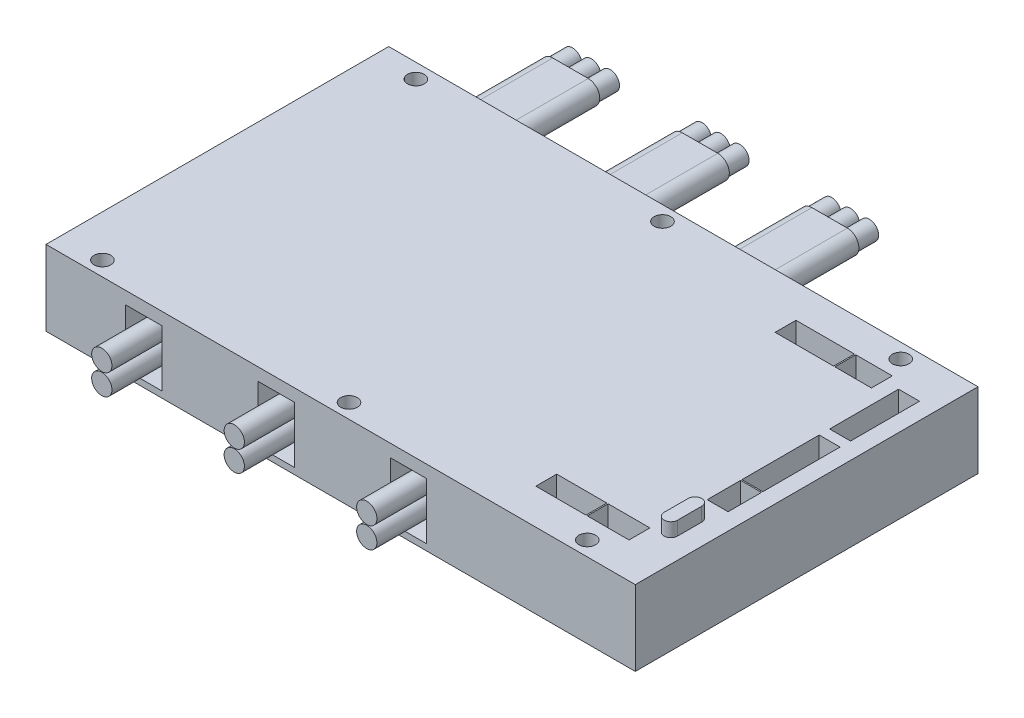
SolidWorks part; units mm, degrees
ref_plane "Front Plane" through (0, 0, 0) normal (0, 0, 1) x (1, 0, 0)
ref_plane "Top Plane" through (0, 0, 0) normal (0, 1, 0) x (1, 0, 0)
ref_plane "Right Plane" through (0, 0, 0) normal (1, 0, 0) x (0, 0, -1)
sketch "Sketch1" plane through (0, 0, 0) normal (0, 1, 0) x (1, 0, 0)
  line L1 (-70.5, -41) -> (70.5, -41)
  line L2 (-70.5, -41) -> (-70.5, 41)
  line L3 (-70.5, 41) -> (70.5, 41)
  line L4 (70.5, -41) -> (70.5, 41)
  line L5 (-70.5, -41) -> (70.5, 41) construction
  line L6 (-70.5, 41) -> (70.5, -41) construction
  point P0 (0, 0)
  dimension "D1" = 82
  dimension "D2" = 141
extrude "Boss-Extrude1" add sketch "Sketch1" along normal mid plane 18
sketch "Sketch3" plane through (0, 9, 0) normal (0, 1, 0) x (1, 0, 0)
  line L0 (-60.5, 37.5) -> (-1.5, 37.5) construction
  line L1 (-1.5, 37.5) -> (55.5, 37.5) construction
  line L2 (70.5, 41) -> (-70.5, 41) construction
  line L3 (-70.5, 41) -> (-70.5, -41) construction
  circle A0 centre (-60.5, 37.5) radius 2
  circle A1 centre (-1.5, 37.5) radius 2
  circle A2 centre (55.5, 37.5) radius 2
  dimension "D1" = 4
  dimension "D2" = 3.5
  dimension "D3" = 10
  dimension "D4" = 59
  dimension "D5" = 57
extrude "Cut-Extrude1" cut sketch "Sketch3" against normal through all
mirror "Mirror1" about plane through (0, 0, 0) normal (0, 0, 1) of "Cut-Extrude1"
sketch "Sketch4" plane through (0, 0, 41) normal (0, 0, 1) x (1, 0, 0)
  line L0 (-47.15, -0.75) -> (-15.45, -0.75) construction
  line L1 (-51.5, -7.5) -> (-42.8, -7.5)
  line L2 (-51.5, -7.5) -> (-51.5, 6)
  line L3 (-51.5, 6) -> (-42.8, 6)
  line L4 (-42.8, -7.5) -> (-42.8, 6)
  line L5 (-51.5, -7.5) -> (-42.8, 6) construction
  line L6 (-51.5, 6) -> (-42.8, -7.5) construction
  line L7 (-19.8, -7.5) -> (-11.1, -7.5)
  line L8 (-19.8, -7.5) -> (-19.8, 6)
  line L9 (-19.8, 6) -> (-11.1, 6)
  line L10 (-11.1, -7.5) -> (-11.1, 6)
  line L11 (-19.8, -7.5) -> (-11.1, 6) construction
  line L12 (-19.8, 6) -> (-11.1, -7.5) construction
  line L13 (11.9, -7.5) -> (20.6, -7.5)
  line L14 (11.9, -7.5) -> (11.9, 6)
  line L15 (11.9, 6) -> (20.6, 6)
  line L16 (20.6, -7.5) -> (20.6, 6)
  line L17 (11.9, -7.5) -> (20.6, 6) construction
  line L18 (11.9, 6) -> (20.6, -7.5) construction
  line L19 (-15.45, -0.75) -> (16.25, -0.75) construction
  line L20 (-70.5, 9) -> (70.5, 9) construction
  line L21 (-70.5, 9) -> (-70.5, -9) construction
  point P0 (-47.15, -0.75)
  point P5 (-15.45, -0.75)
  point P10 (16.25, -0.75)
  dimension "D1" = 13.5
  dimension "D2" = 8.7
  dimension "D3" = 3
  dimension "D4" = 19
  dimension "D5" = 23
extrude "Cut-Extrude2" cut sketch "Sketch4" against normal blind 10
sketch "Sketch5" plane through (0, 0, -41) normal (0, 0, -1) x (-1, 0, 0)
  line L0 (47, 3.5) -> (16, 3.5) construction
  line L1 (37, 1) -> (57, 1)
  line L2 (37, 1) -> (37, 6)
  line L3 (37, 6) -> (57, 6)
  line L4 (57, 1) -> (57, 6)
  line L5 (37, 1) -> (57, 6) construction
  line L6 (37, 6) -> (57, 1) construction
  line L7 (6, 1) -> (26, 1)
  line L8 (6, 1) -> (6, 6)
  line L9 (6, 6) -> (26, 6)
  line L10 (26, 1) -> (26, 6)
  line L11 (6, 1) -> (26, 6) construction
  line L12 (6, 6) -> (26, 1) construction
  line L13 (-25, 1) -> (-5, 1)
  line L14 (-25, 1) -> (-25, 6)
  line L15 (-25, 6) -> (-5, 6)
  line L16 (-5, 1) -> (-5, 6)
  line L17 (-25, 1) -> (-5, 6) construction
  line L18 (-25, 6) -> (-5, 1) construction
  line L19 (16, 3.5) -> (-15, 3.5) construction
  line L20 (-70.5, 9) -> (70.5, 9) construction
  line L21 (70.5, 9) -> (70.5, -9) construction
  point P0 (47, 3.5)
  point P5 (16, 3.5)
  point P10 (-15, 3.5)
  dimension "D1" = 3
  dimension "D2" = 5
  dimension "D3" = 20
  dimension "D4" = 13.5
  dimension "D5" = 11
extrude "Cut-Extrude3" cut sketch "Sketch5" against normal blind 10
sketch "Sketch6" plane through (0, 9, 0) normal (0, 1, 0) x (1, 0, 0)
  line L0 (-70.5, -41) -> (70.5, -41) construction
  line L1 (62.27, -25.885) -> (65.5, -25.885)
  line L2 (62.27, -25.885) -> (62.27, -20.115)
  line L3 (62.27, -20.115) -> (65.5, -20.115)
  line L4 (65.5, -25.885) -> (65.5, -20.115)
  line L5 (62.27, -25.885) -> (65.5, -20.115) construction
  line L6 (62.27, -20.115) -> (65.5, -25.885) construction
  line L7 (70.5, -41) -> (70.5, 41) construction
  arc A0 (65.5, -20.115) -> (62.27, -20.115) centre (63.885, -20.115) ccw
  arc A1 (65.5, -25.885) -> (62.27, -25.885) centre (63.885, -25.885) cw
  point P0 (63.885, -23)
  point P9 (63.885, -18.5)
  point P10 (63.885, -27.5)
  dimension "D1" = 3.23
  dimension "D2" = 9
  dimension "D3" = 13.5
  dimension "D4" = 5
extrude "Boss-Extrude2" add sketch "Sketch6" along normal blind 3.3 contours L1 L4 L3 L2 | L3 A0 | A1 L1
sketch "Sketch7" plane through (0, 0, 31) normal (0, 0, 1) x (1, 0, 0)
  line L0 (-47.15, 1.75) -> (-47.15, 6) construction
  line L1 (-42.8, 6) -> (-51.5, 6) construction
  line L2 (-47.15, 1.75) -> (-47.15, -3.25) construction
  line L3 (-47.15, -3.25) -> (-47.15, -7.5) construction
  line L4 (-51.5, -7.5) -> (-42.8, -7.5) construction
  circle A0 centre (-47.15, 1.75) radius 2.425
  circle A1 centre (-47.15, -3.25) radius 2.425
  dimension "D1" = 4.85
  dimension "D2" = 5
extrude "Boss-Extrude3" add sketch "Sketch7" along normal blind 20
pattern_linear "LPattern1" count 3 spacing 31.7 along (1, 0, 0) of "Boss-Extrude3"
sketch "Sketch8" plane through (0, 0, -31) normal (0, 0, -1) x (-1, 0, 0)
  line L0 (47, 3.5) -> (47, 6) construction
  line L1 (42.75, 0.75) -> (51.25, 0.75)
  line L2 (42.75, 0.75) -> (42.75, 6.25)
  line L3 (42.75, 6.25) -> (51.25, 6.25)
  line L4 (51.25, 0.75) -> (51.25, 6.25)
  line L5 (42.75, 0.75) -> (51.25, 6.25) construction
  line L6 (42.75, 6.25) -> (51.25, 0.75) construction
  line L7 (57, 6) -> (37, 6) construction
  line L8 (47, 3.5) -> (47, 1) construction
  line L9 (37, 1) -> (57, 1) construction
  arc A0 (51.25, 6.25) -> (51.25, 0.75) centre (51.25, 3.5) cw
  arc A1 (42.75, 6.25) -> (42.75, 0.75) centre (42.75, 3.5) ccw
  point P0 (47, 3.5)
  point P9 (40, 3.5)
  point P10 (54, 3.5)
  line M7 (57, 6) -> (37, 6)
  line M9 (37, 1) -> (57, 1)
  dimension "D1" = 14
  dimension "D2" = 5.5
extrude "Boss-Extrude4" add sketch "Sketch8" along normal blind 30 contours L4 L2 M9 M7 | A0 L4 M7 M9 | A1 L2 M7 M9 | L4 L3 L2 M7 | A0 L4 M7 | L2 A1 M7 | A1 L2 M9 | L1 L4 L2 M9 | A0 L4 M9
sketch "Sketch10" plane through (0, 0, -61) normal (0, 0, -1) x (-1, 0, 0)
  line L0 (42.75, 0.75) -> (51.25, 0.75) construction
  line L1 (42.75, 6.25) -> (51.25, 6.25) construction
  line L2 (42.75, 0.75) -> (51.25, 0.75) construction
  line L3 (42.75, 6.25) -> (51.25, 6.25) construction
  line L4 (42.5, 3.5) -> (47, 3.5) construction
  line L5 (47, 3.5) -> (51.5, 3.5) construction
  line L6 (47, 3.5) -> (47, 6.25) construction
  line L7 (47, 3.5) -> (47, 0.75) construction
  circle A0 centre (51.5, 3.5) radius 2.225
  circle A1 centre (47, 3.5) radius 2.225
  circle A2 centre (42.5, 3.5) radius 2.225
  dimension "D1" = 4.45
  dimension "D2" = 4.5
extrude "Boss-Extrude6" add sketch "Sketch10" along normal blind 5
pattern_linear "LPattern2" count 3 spacing 31 along (1, 0, 0) of "Boss-Extrude4", "Boss-Extrude6"
sketch "Sketch9" plane through (0, 9, 0) normal (0, 1, 0) x (1, 0, 0)
  line L0 (44.2, -30) -> (55.5, -30) construction
  line L1 (38.2, -32.5) -> (50.2, -32.5)
  line L2 (38.2, -32.5) -> (38.2, -27.5)
  line L3 (38.2, -27.5) -> (50.2, -27.5)
  line L4 (50.2, -32.5) -> (50.2, -27.5)
  line L5 (38.2, -32.5) -> (50.2, -27.5) construction
  line L6 (38.2, -27.5) -> (50.2, -32.5) construction
  line L11 (60.5, -32.5) -> (50.5, -32.5)
  line L12 (60.5, -32.5) -> (60.5, -27.5)
  line L13 (60.5, -27.5) -> (50.5, -27.5)
  line L14 (50.5, -32.5) -> (50.5, -27.5)
  line L15 (60.5, -32.5) -> (50.5, -27.5) construction
  line L16 (60.5, -27.5) -> (50.5, -32.5) construction
  line L17 (41.95, 30.5) -> (53.625, 30.5) construction
  line L18 (61.5, -14.8) -> (66.5, -14.8)
  line L19 (61.5, -14.8) -> (61.5, -6.8)
  line L20 (61.5, -6.8) -> (66.5, -6.8)
  line L21 (66.5, -14.8) -> (66.5, -6.8)
  line L22 (61.5, -14.8) -> (66.5, -6.8) construction
  line L23 (61.5, -6.8) -> (66.5, -14.8) construction
  line L24 (66.5, 12) -> (61.5, 12)
  line L25 (66.5, 12) -> (66.5, -6.5)
  line L26 (66.5, -6.5) -> (61.5, -6.5)
  line L27 (61.5, 12) -> (61.5, -6.5)
  line L28 (66.5, 12) -> (61.5, -6.5) construction
  line L29 (66.5, -6.5) -> (61.5, 12) construction
  line L30 (66.5, 31) -> (61.5, 31)
  line L31 (66.5, 31) -> (66.5, 14.5)
  line L32 (66.5, 14.5) -> (61.5, 14.5)
  line L33 (61.5, 31) -> (61.5, 14.5)
  line L34 (66.5, 31) -> (61.5, 14.5) construction
  line L35 (66.5, 14.5) -> (61.5, 31) construction
  line L36 (49.25, 28) -> (58, 28)
  line L37 (49.25, 28) -> (49.25, 33)
  line L38 (49.25, 33) -> (58, 33)
  line L39 (58, 28) -> (58, 33)
  line L40 (49.25, 28) -> (58, 33) construction
  line L41 (49.25, 33) -> (58, 28) construction
  line L42 (34.95, 28) -> (48.95, 28)
  line L43 (34.95, 28) -> (34.95, 33)
  line L44 (34.95, 33) -> (48.95, 33)
  line L45 (48.95, 28) -> (48.95, 33)
  line L46 (34.95, 28) -> (48.95, 33) construction
  line L47 (34.95, 33) -> (48.95, 28) construction
  line L48 (64, 22.75) -> (64, 2.75) construction
  line L49 (64, 2.75) -> (64, -10.8) construction
  line L50 (70.5, -41) -> (70.5, 41) construction
  line L51 (70.5, 41) -> (-70.5, 41) construction
  line L52 (-70.5, -41) -> (70.5, -41) construction
  point P0 (44.2, -30)
  point P5 (55.5, -30)
  point P12 (64, -10.8)
  point P17 (64, 2.75)
  point P22 (64, 22.75)
  point P27 (53.625, 30.5)
  point P32 (41.95, 30.5)
  point P46 (64, 8.1688)
  point P47 (0, 0)
  dimension "D1" = 14
  dimension "D2" = 8.75
  dimension "D3" = 0.3
  dimension "D4" = 12.5
  dimension "D5" = 8
  dimension "D6" = 5
  dimension "D7" = 16.5
  dimension "D8" = 4
  dimension "D9" = 10
  dimension "D10" = 2.5
  dimension "D11" = 0.3
  dimension "D12" = 18.5
  dimension "D13" = 8
  dimension "D14" = 8.5
  dimension "D15" = 10
  dimension "D16" = 0.3
  dimension "D17" = 10
  dimension "D18" = 12
extrude "Cut-Extrude4" cut sketch "Sketch9" against normal blind 5
